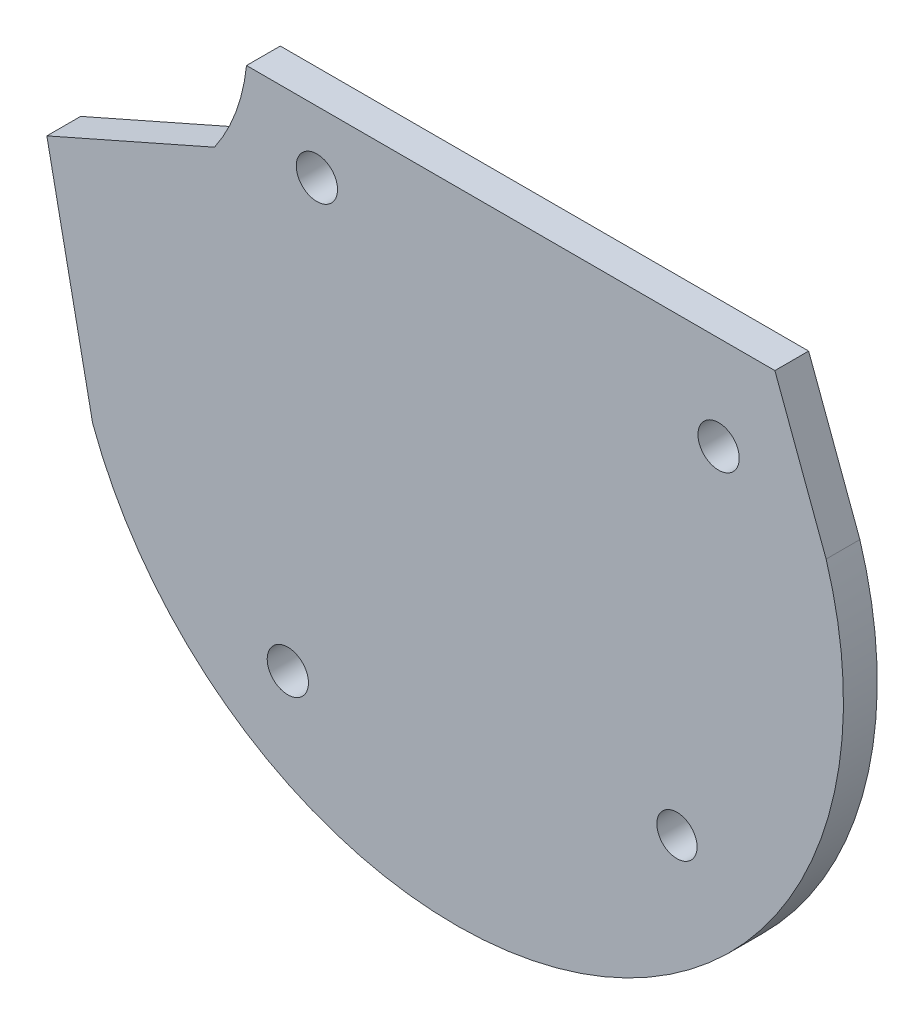
SolidWorks part; units mm, degrees
ref_plane "Front Plane" through (0, 0, 0) normal (0, 0, 1) x (1, 0, 0)
ref_plane "Top Plane" through (0, 0, 0) normal (0, 1, 0) x (1, 0, 0)
ref_plane "Right Plane" through (0, 0, 0) normal (1, 0, 0) x (0, 0, -1)
sketch "Sketch5" plane through (0, 0, 0) normal (0, 0, -1) x (-0.0184, 0.9998, 0)
  line L0 (33.8067, 26.1862) -> (34.4639, -9.5778)
  line L1 (28.6302, -11.8533) -> (23.8302, -23.2927)
  line L2 (23.8302, -23.2927) -> (8.4862, -20.4775)
  line L3 (33.8067, 26.1862) -> (24.4257, 29.4824)
  line L4 (30.1797, -4.8908) -> (34.3764, -4.8137) construction
  line L5 (34.3764, -4.8137) -> (34.4639, -9.5778) construction
  line L6 (34.4639, -9.5778) -> (34.3766, -9.5968) construction
  line L7 (27.5277, 22.2602) -> (33.8767, 22.3769) construction
  line L8 (27.5277, 22.2602) -> (27.4143, 28.4323) construction
  line L9 (3.3631, 18.996) -> (-4.6952, 18.8479) construction
  line L10 (3.3631, 18.996) -> (3.2246, 26.5341) construction
  line L11 (30.1797, -4.8908) -> (30.2892, -10.847) construction
  line L12 (0.3178, -7.4078) -> (0.4754, -15.9798) construction
  line L13 (0.3178, -7.4078) -> (-6.2927, -7.5293) construction
  arc A0 (34.4639, -9.5778) -> (28.6302, -11.8533) centre (36.0016, -22.1359) ccw
  arc A1 (24.4257, 29.4824) -> (8.4862, -20.4775) centre (17.1235, 4.2895) ccw
  circle A2 centre (27.5277, 22.2602) radius 1.397
  circle A3 centre (30.1797, -4.8908) radius 1.397
  circle A4 centre (3.3631, 18.996) radius 1.3622
  circle A5 centre (0.3178, -7.4078) radius 1.397
extrude "Extrude1" add sketch "Sketch5" along normal blind 2.286
sketch "Sketch9" plane through (0, 0, -2.286) normal (0, 0, -1) x (-1, 0, 0)
  line L0 (-25.5606, 34.2821) -> (-4.7199, 34.2821) construction
  line L1 (10.2095, 34.2821) -> (-25.5606, 34.2821) construction
  line L2 (-4.7199, 34.2821) -> (-4.7199, 11.9301) construction
  line L3 (-4.7199, 34.2821) -> (10.2095, 34.2821) construction
  line L4 (7.4124, 0.1817) -> (4.586, 2.9187) construction
